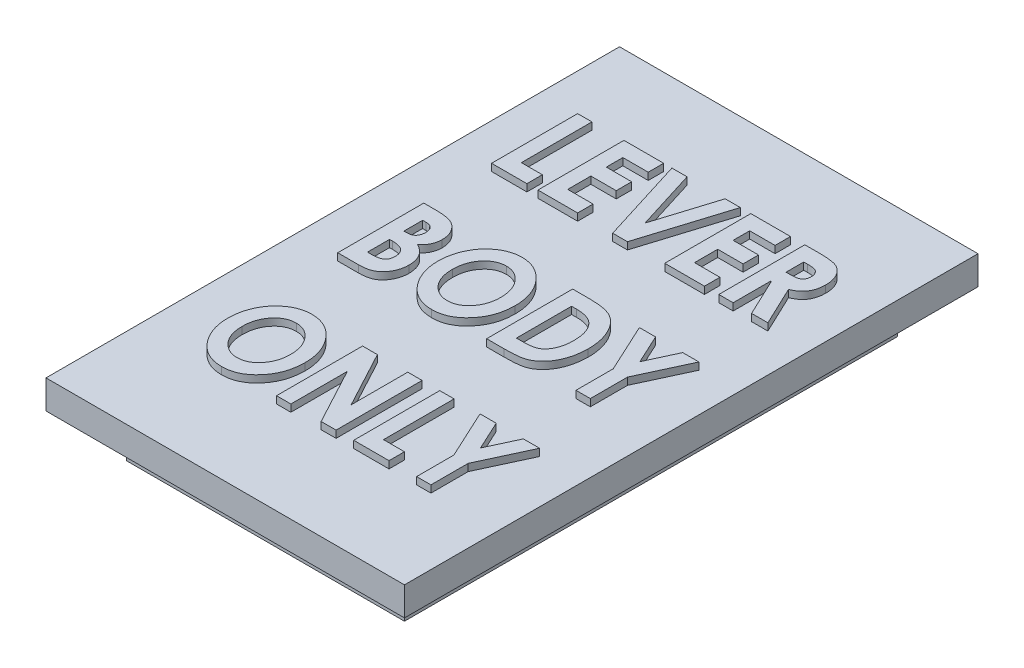
SolidWorks part; units mm, degrees
ref_plane "Front Plane" through (0, 0, 0) normal (0, 0, 1) x (1, 0, 0)
ref_plane "Top Plane" through (0, 0, 0) normal (0, 1, 0) x (1, 0, 0)
ref_plane "Right Plane" through (0, 0, 0) normal (1, 0, 0) x (0, 0, -1)
sketch "Sketch1" plane through (0, 0, 0) normal (0, 1, 0) x (1, 0, 0)
  line L1 (9.7, -17.2) -> (-9.7, -17.2)
  line L2 (9.7, -17.2) -> (9.7, 17.2)
  line L3 (9.7, 17.2) -> (-9.7, 17.2)
  line L4 (-9.7, -17.2) -> (-9.7, 17.2)
  line L5 (9.7, -17.2) -> (-9.7, 17.2) construction
  line L6 (9.7, 17.2) -> (-9.7, -17.2) construction
  point P0 (0, 0)
  dimension "D1" = 19.4
  dimension "D2" = 34.4
extrude "Boss-Extrude1" add sketch "Sketch1" along normal blind 3
sketch "Sketch2" plane through (0, 3, 0) normal (0, 1, 0) x (1, 0, 0)
  line L1 (12.5, -20) -> (-12.5, -20)
  line L2 (12.5, -20) -> (12.5, 20)
  line L3 (12.5, 20) -> (-12.5, 20)
  line L4 (-12.5, -20) -> (-12.5, 20)
  line L5 (12.5, -20) -> (-12.5, 20) construction
  line L6 (12.5, 20) -> (-12.5, -20) construction
  point P0 (0, 0)
  dimension "D1" = 25
  dimension "D2" = 40
extrude "Boss-Extrude2" add sketch "Sketch2" along normal blind 2
sketch "Sketch3" plane through (0, 5, 0) normal (0, 1, 0) x (1, 0, 0)
  line L0 (-12.5, 8) -> (12.5, 8) construction
  line L1 (-12.5, 20) -> (-12.5, -20) construction
  line L2 (12.5, -20) -> (12.5, 20) construction
  line L3 (12.5, 20) -> (-12.5, 20) construction
  text T0 "<b>LEVER</b>\r\n<b>BODY</b>\r\n<b>ONLY</b>" font "Century Gothic" height 6
  dimension "D1" = 12
extrude "Boss-Extrude3" add sketch "Sketch3" along normal blind 0.5
